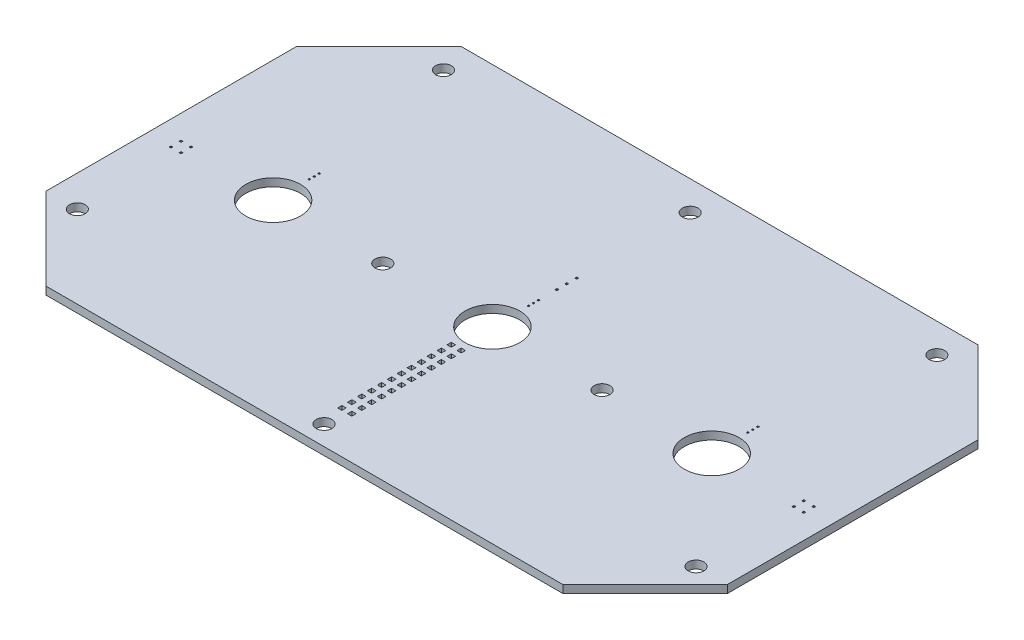
SolidWorks part; units mm, degrees
ref_plane "前视基准面" through (0, 0, 0) normal (0, 0, 1) x (1, 0, 0)
ref_plane "上视基准面" through (0, 0, 0) normal (0, 1, 0) x (1, 0, 0)
ref_plane "右视基准面" through (0, 0, 0) normal (1, 0, 0) x (0, 0, -1)
sketch "草图1" plane through (0, 0, 0) normal (0, 1, 0) x (1, 0, 0)
  line L0 (-87, 32) -> (-66, 53)
  line L1 (-87, -53) -> (87, -53)
  line L2 (-87, -53) -> (-87, 53)
  line L3 (-87, 53) -> (87, 53)
  line L4 (87, -53) -> (87, 53)
  line L5 (-87, -53) -> (87, 53) construction
  line L6 (-87, 53) -> (87, -53) construction
  line L7 (66, 53) -> (87, 32)
  line L8 (-87, -32) -> (-66, -53)
  line L9 (66, -53) -> (87, -32)
  point P0 (0, 0)
  dimension "D1" = 174
  dimension "D2" = 106
  dimension "D3" = 21
  dimension "D4" = 21
  dimension "D5" = 21
  dimension "D6" = 21
extrude "凸台-拉伸1" add sketch "草图1" along normal blind 2 contours L1 L9 L4 L7 L3 L0 L2 L8
sketch "草图2" plane through (0, 2, 0) normal (0, 1, 0) x (1, 0, 0)
  line L0 (-104.4582, -5) -> (111.7232, -5) construction
  line L1 (0, 63.8138) -> (0, -72.6495) construction
  line L2 (-85.6086, 45.5) -> (100.9239, 45.5) construction
  line L3 (-66, -53) -> (66, -53) construction
  line L4 (-66, 53) -> (66, 53) construction
  circle A0 centre (0, 45.5) radius 2
  circle A1 centre (63, 45.5) radius 2
  circle A2 centre (-63, 45.5) radius 2
  circle A3 centre (-69.5, -5) radius 2
  circle A4 centre (-42.5, -5) radius 2
  circle A5 centre (-28, -5) radius 2
  circle A6 centre (-13.5, -5) radius 2
  circle A7 centre (13.5, -5) radius 2
  circle A8 centre (28, -5) radius 2
  circle A9 centre (42.5, -5) radius 2
  circle A10 centre (69.5, -5) radius 2
  circle A11 centre (79, -32) radius 2
  circle A12 centre (-79, -32) radius 2
  circle A13 centre (0, -48) radius 2
  dimension "D3" = 63
  dimension "D6" = 4
  dimension "D9" = 5
  dimension "D1" = 48
  dimension "D2" = 7.5
  dimension "D4" = 63
  dimension "D5" = 21
  dimension "D7" = 158
  dimension "D8" = 79
  dimension "D10" = 13.5
  dimension "D11" = 13.5
  dimension "D12" = 27
  dimension "D13" = 27
  dimension "D14" = 85
  dimension "D15" = 42.5
  dimension "D16" = 28
  dimension "D17" = 28
sketch "草图7" plane through (0, 2, 0) normal (0, 1, 0) x (1, 0, 0)
  circle A0 centre (-56, -5) radius 7
  circle A1 centre (63, 45.5) radius 2
  circle A2 centre (63, 45.5) radius 2
  circle A3 centre (0, 45.5) radius 2
  circle A4 centre (0, 45.5) radius 2
  circle A5 centre (42.5, -5) radius 2
  circle A6 centre (42.5, -5) radius 2
  circle A7 centre (28, -5) radius 2
  circle A8 centre (28, -5) radius 2
  circle A9 centre (13.5, -5) radius 2
  circle A10 centre (13.5, -5) radius 2
  circle A11 centre (-13.5, -5) radius 2
  circle A12 centre (-13.5, -5) radius 2
  circle A13 centre (-28, -5) radius 2
  circle A14 centre (-28, -5) radius 2
  circle A15 centre (-42.5, -5) radius 2
  circle A16 centre (-42.5, -5) radius 2
  circle A17 centre (-69.5, -5) radius 2
  circle A18 centre (-69.5, -5) radius 2
  circle A19 centre (-63, 45.5) radius 2
  circle A20 centre (-63, 45.5) radius 2
  circle A21 centre (0, -48) radius 2
  circle A22 centre (0, -48) radius 2
  circle A23 centre (-79, -32) radius 2
  circle A24 centre (-79, -32) radius 2
  circle A25 centre (79, -32) radius 2
  circle A26 centre (79, -32) radius 2
  circle A27 centre (69.5, -5) radius 2
  circle A28 centre (69.5, -5) radius 2
  circle A29 centre (0, -5) radius 7
  circle A30 centre (56, -5) radius 7
  dimension "D15" = 13.5
  dimension "D16" = 14
  dimension "D17" = 13.5
  dimension "D1" = 0
  dimension "D2" = 0
  dimension "D3" = 0
  dimension "D4" = 0
  dimension "D5" = 0
  dimension "D6" = 0
  dimension "D7" = 0
  dimension "D8" = 0
  dimension "D9" = 0
  dimension "D10" = 0
  dimension "D11" = 0
  dimension "D12" = 0
  dimension "D13" = 0
  dimension "D14" = 0
extrude "切除-拉伸3" cut sketch "草图7" against normal through all contours A0 | A29 | A30
extrude "切除-拉伸4" cut sketch "草图2" against normal through all contours A2 | A0 | A1 | A8 | A5 | A12 | A13 | A11
sketch "草图8" plane through (0, 2, 0) normal (0, 1, 0) x (1, 0, 0)
  line L16 (-0.72, -32.56) -> (-0.72, -31.46)
  line L17 (-1.82, -32.56) -> (-0.72, -32.56)
  line L18 (-1.82, -31.46) -> (-1.82, -32.56)
  line L19 (-0.72, -31.46) -> (-1.82, -31.46)
  line L24 (-0.72, -35.1) -> (-0.72, -34)
  line L25 (-1.82, -35.1) -> (-0.72, -35.1)
  line L26 (-1.82, -34) -> (-1.82, -35.1)
  line L27 (-0.72, -34) -> (-1.82, -34)
  line L32 (-0.72, -37.64) -> (-0.72, -36.54)
  line L33 (-1.82, -37.64) -> (-0.72, -37.64)
  line L34 (-1.82, -36.54) -> (-1.82, -37.64)
  line L35 (-0.72, -36.54) -> (-1.82, -36.54)
  line L40 (-0.72, -40.18) -> (-0.72, -39.08)
  line L41 (-1.82, -40.18) -> (-0.72, -40.18)
  line L42 (-1.82, -39.08) -> (-1.82, -40.18)
  line L43 (-0.72, -39.08) -> (-1.82, -39.08)
  line L48 (1.82, -14.78) -> (1.82, -13.68)
  line L49 (0.72, -14.78) -> (1.82, -14.78)
  line L50 (0.72, -13.68) -> (0.72, -14.78)
  line L51 (1.82, -13.68) -> (0.72, -13.68)
  line L56 (1.82, -17.32) -> (1.82, -16.22)
  line L57 (0.72, -17.32) -> (1.82, -17.32)
  line L58 (0.72, -16.22) -> (0.72, -17.32)
  line L59 (1.82, -16.22) -> (0.72, -16.22)
  line L64 (1.82, -19.86) -> (1.82, -18.76)
  line L65 (0.72, -19.86) -> (1.82, -19.86)
  line L66 (0.72, -18.76) -> (0.72, -19.86)
  line L67 (1.82, -18.76) -> (0.72, -18.76)
  line L72 (1.82, -22.4) -> (1.82, -21.3)
  line L73 (0.72, -22.4) -> (1.82, -22.4)
  line L74 (0.72, -21.3) -> (0.72, -22.4)
  line L75 (1.82, -21.3) -> (0.72, -21.3)
  line L80 (1.82, -24.94) -> (1.82, -23.84)
  line L81 (0.72, -24.94) -> (1.82, -24.94)
  line L82 (0.72, -23.84) -> (0.72, -24.94)
  line L83 (1.82, -23.84) -> (0.72, -23.84)
  line L88 (1.82, -27.48) -> (1.82, -26.38)
  line L89 (0.72, -27.48) -> (1.82, -27.48)
  line L90 (0.72, -26.38) -> (0.72, -27.48)
  line L91 (1.82, -26.38) -> (0.72, -26.38)
  line L96 (1.82, -30.02) -> (1.82, -28.92)
  line L97 (0.72, -30.02) -> (1.82, -30.02)
  line L98 (0.72, -28.92) -> (0.72, -30.02)
  line L99 (1.82, -28.92) -> (0.72, -28.92)
  line L104 (1.82, -32.56) -> (1.82, -31.46)
  line L105 (0.72, -32.56) -> (1.82, -32.56)
  line L106 (0.72, -31.46) -> (0.72, -32.56)
  line L107 (1.82, -31.46) -> (0.72, -31.46)
  line L112 (1.82, -35.1) -> (1.82, -34)
  line L113 (0.72, -35.1) -> (1.82, -35.1)
  line L114 (0.72, -34) -> (0.72, -35.1)
  line L115 (1.82, -34) -> (0.72, -34)
  line L120 (1.82, -37.64) -> (1.82, -36.54)
  line L121 (0.72, -37.64) -> (1.82, -37.64)
  line L122 (0.72, -36.54) -> (0.72, -37.64)
  line L123 (1.82, -36.54) -> (0.72, -36.54)
  line L128 (1.82, -40.18) -> (1.82, -39.08)
  line L129 (0.72, -40.18) -> (1.82, -40.18)
  line L130 (0.72, -39.08) -> (0.72, -40.18)
  line L131 (1.82, -39.08) -> (0.72, -39.08)
  line L136 (1.82, -42.72) -> (1.82, -41.62)
  line L137 (0.72, -42.72) -> (1.82, -42.72)
  line L138 (0.72, -41.62) -> (0.72, -42.72)
  line L139 (1.82, -41.62) -> (0.72, -41.62)
  line L144 (-0.72, -30.02) -> (-0.72, -28.92)
  line L145 (-1.82, -30.02) -> (-0.72, -30.02)
  line L146 (-1.82, -28.92) -> (-1.82, -30.02)
  line L147 (-0.72, -28.92) -> (-1.82, -28.92)
  line L152 (-0.72, -27.48) -> (-0.72, -26.38)
  line L153 (-1.82, -27.48) -> (-0.72, -27.48)
  line L154 (-1.82, -26.38) -> (-1.82, -27.48)
  line L155 (-0.72, -26.38) -> (-1.82, -26.38)
  line L160 (-0.72, -24.94) -> (-0.72, -23.84)
  line L161 (-1.82, -24.94) -> (-0.72, -24.94)
  line L162 (-1.82, -23.84) -> (-1.82, -24.94)
  line L163 (-0.72, -23.84) -> (-1.82, -23.84)
  line L168 (-0.72, -22.4) -> (-0.72, -21.3)
  line L169 (-1.82, -22.4) -> (-0.72, -22.4)
  line L170 (-1.82, -21.3) -> (-1.82, -22.4)
  line L171 (-0.72, -21.3) -> (-1.82, -21.3)
  line L176 (-0.72, -19.86) -> (-0.72, -18.76)
  line L177 (-1.82, -19.86) -> (-0.72, -19.86)
  line L178 (-1.82, -18.76) -> (-1.82, -19.86)
  line L179 (-0.72, -18.76) -> (-1.82, -18.76)
  line L184 (-0.72, -17.32) -> (-0.72, -16.22)
  line L185 (-1.82, -17.32) -> (-0.72, -17.32)
  line L186 (-1.82, -16.22) -> (-1.82, -17.32)
  line L187 (-0.72, -16.22) -> (-1.82, -16.22)
  line L192 (-0.72, -14.78) -> (-0.72, -13.68)
  line L193 (-1.82, -14.78) -> (-0.72, -14.78)
  line L194 (-1.82, -13.68) -> (-1.82, -14.78)
  line L195 (-0.72, -13.68) -> (-1.82, -13.68)
  line L200 (-0.72, -42.72) -> (-0.72, -41.62)
  line L201 (-1.82, -42.72) -> (-0.72, -42.72)
  line L202 (-1.82, -41.62) -> (-1.82, -42.72)
  line L203 (-0.72, -41.62) -> (-1.82, -41.62)
extrude "切除-拉伸5" cut sketch "草图8" against normal blind 10
sketch "草图9" plane through (0, 2, 0) normal (0, 1, 0) x (1, 0, 0)
  line L44 (81.04, -3.98) -> (81.04, -3.48)
  line L45 (81.04, -3.48) -> (80.54, -3.48)
  line L46 (80.54, -3.48) -> (80.54, -3.98)
  line L47 (80.54, -3.98) -> (81.04, -3.98)
  line L48 (78.5, -3.98) -> (78.5, -3.48)
  line L49 (78.5, -3.48) -> (78, -3.48)
  line L50 (78, -3.48) -> (78, -3.98)
  line L51 (78, -3.98) -> (78.5, -3.98)
  line L52 (78.5, -6.52) -> (78.5, -6.02)
  line L53 (78.5, -6.02) -> (78, -6.02)
  line L54 (78, -6.02) -> (78, -6.52)
  line L55 (78, -6.52) -> (78.5, -6.52)
  line L56 (81.04, -6.52) -> (81.04, -6.02)
  line L57 (81.04, -6.02) -> (80.54, -6.02)
  line L58 (80.54, -6.02) -> (80.54, -6.52)
  line L59 (80.54, -6.52) -> (81.04, -6.52)
  line L60 (-0.25, 16.79) -> (-0.25, 16.29)
  line L61 (-0.25, 16.29) -> (0.25, 16.29)
  line L62 (0.25, 16.29) -> (0.25, 16.79)
  line L63 (0.25, 16.79) -> (-0.25, 16.79)
  line L64 (-0.25, 14.25) -> (-0.25, 13.75)
  line L65 (-0.25, 13.75) -> (0.25, 13.75)
  line L66 (0.25, 13.75) -> (0.25, 14.25)
  line L67 (0.25, 14.25) -> (-0.25, 14.25)
  line L68 (-0.25, 11.71) -> (-0.25, 11.21)
  line L69 (-0.25, 11.21) -> (0.25, 11.21)
  line L70 (0.25, 11.21) -> (0.25, 11.71)
  line L71 (0.25, 11.71) -> (-0.25, 11.71)
  line L72 (-81.04, -3.48) -> (-81.04, -3.98)
  line L73 (-81.04, -3.98) -> (-80.54, -3.98)
  line L74 (-80.54, -3.98) -> (-80.54, -3.48)
  line L75 (-80.54, -3.48) -> (-81.04, -3.48)
  line L76 (-78.5, -3.48) -> (-78.5, -3.98)
  line L77 (-78.5, -3.98) -> (-78, -3.98)
  line L78 (-78, -3.98) -> (-78, -3.48)
  line L79 (-78, -3.48) -> (-78.5, -3.48)
  line L80 (-81.04, -6.02) -> (-81.04, -6.52)
  line L81 (-81.04, -6.52) -> (-80.54, -6.52)
  line L82 (-80.54, -6.52) -> (-80.54, -6.02)
  line L83 (-80.54, -6.02) -> (-81.04, -6.02)
  line L84 (-78.5, -6.02) -> (-78.5, -6.52)
  line L85 (-78.5, -6.52) -> (-78, -6.52)
  line L86 (-78, -6.52) -> (-78, -6.02)
  line L87 (-78, -6.02) -> (-78.5, -6.02)
  line L100 (56.2, 6.57) -> (55.8, 6.57)
  line L101 (55.8, 6.57) -> (55.8, 6.97)
  line L102 (55.8, 6.97) -> (56.2, 6.97)
  line L103 (56.2, 6.97) -> (56.2, 6.57)
  line L104 (56.2, 5.3) -> (55.8, 5.3)
  line L105 (55.8, 5.3) -> (55.8, 5.7)
  line L106 (55.8, 5.7) -> (56.2, 5.7)
  line L107 (56.2, 5.7) -> (56.2, 5.3)
  line L108 (56.2, 4.03) -> (55.8, 4.03)
  line L109 (55.8, 4.03) -> (55.8, 4.43)
  line L110 (55.8, 4.43) -> (56.2, 4.43)
  line L111 (56.2, 4.43) -> (56.2, 4.03)
  line L124 (0.2, 6.57) -> (-0.2, 6.57)
  line L125 (-0.2, 6.57) -> (-0.2, 6.97)
  line L126 (-0.2, 6.97) -> (0.2, 6.97)
  line L127 (0.2, 6.97) -> (0.2, 6.57)
  line L128 (0.2, 5.3) -> (-0.2, 5.3)
  line L129 (-0.2, 5.3) -> (-0.2, 5.7)
  line L130 (-0.2, 5.7) -> (0.2, 5.7)
  line L131 (0.2, 5.7) -> (0.2, 5.3)
  line L132 (0.2, 4.03) -> (-0.2, 4.03)
  line L133 (-0.2, 4.03) -> (-0.2, 4.43)
  line L134 (-0.2, 4.43) -> (0.2, 4.43)
  line L135 (0.2, 4.43) -> (0.2, 4.03)
  line L148 (-55.8, 6.57) -> (-56.2, 6.57)
  line L149 (-56.2, 6.57) -> (-56.2, 6.97)
  line L150 (-56.2, 6.97) -> (-55.8, 6.97)
  line L151 (-55.8, 6.97) -> (-55.8, 6.57)
  line L152 (-55.8, 5.3) -> (-56.2, 5.3)
  line L153 (-56.2, 5.3) -> (-56.2, 5.7)
  line L154 (-56.2, 5.7) -> (-55.8, 5.7)
  line L155 (-55.8, 5.7) -> (-55.8, 5.3)
  line L156 (-55.8, 4.03) -> (-56.2, 4.03)
  line L157 (-56.2, 4.03) -> (-56.2, 4.43)
  line L158 (-56.2, 4.43) -> (-55.8, 4.43)
  line L159 (-55.8, 4.43) -> (-55.8, 4.03)
extrude "切除-拉伸6" cut sketch "草图9" against normal blind 10
